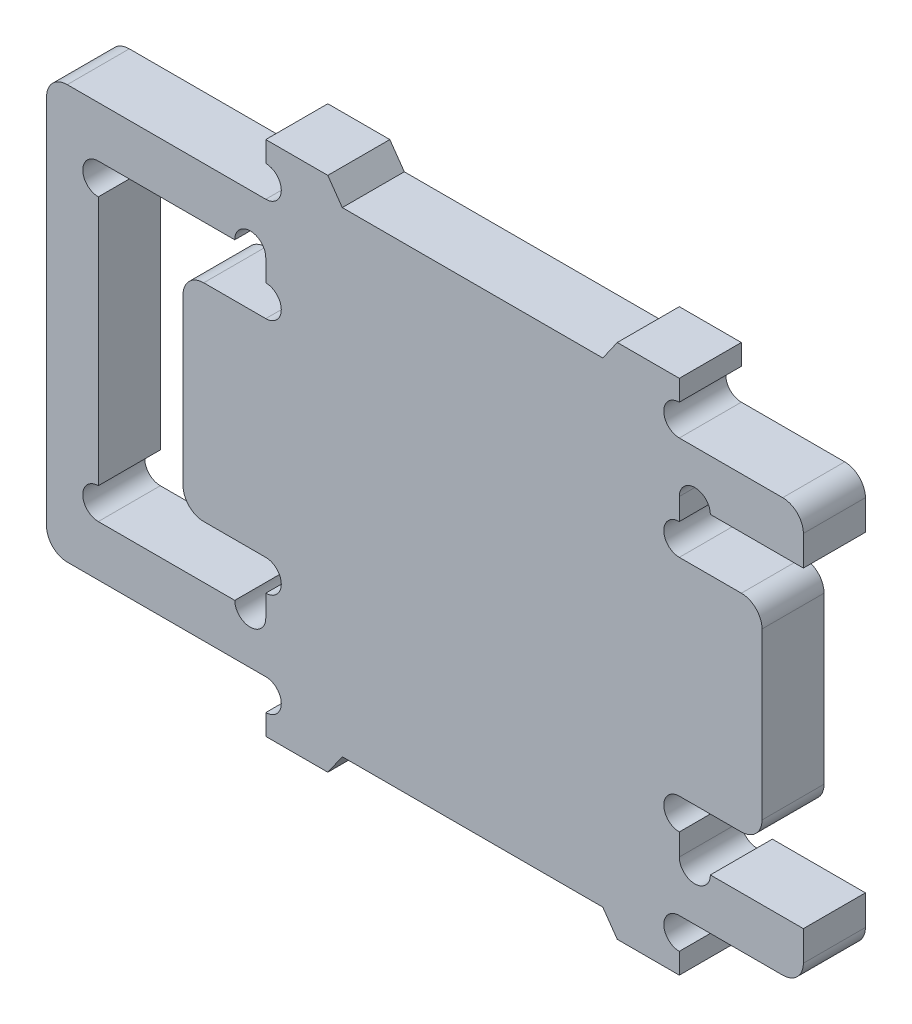
SolidWorks part; units mm, degrees
ref_plane "前视基准面" through (0, 0, 0) normal (0, 0, 1) x (1, 0, 0)
ref_plane "上视基准面" through (0, 0, 0) normal (0, 1, 0) x (1, 0, 0)
ref_plane "右视基准面" through (0, 0, 0) normal (1, 0, 0) x (0, 0, -1)
sketch "草图1" plane through (0, 0, 0) normal (0, 0, 1) x (1, 0, 0)
  line L0 (0, 10) -> (10.6, 10)
  line L1 (0, 10) -> (0, -10)
  line L2 (0, -10) -> (10.6, -10)
  line L3 (6.6, 5) -> (10.6, 5)
  line L4 (6.6, 5) -> (6.6, -5)
  line L5 (6.6, -5) -> (10.6, -5)
  line L6 (2.5, 7.55) -> (10.6, 7.55)
  line L7 (2.5, 7.55) -> (2.5, -7.55)
  line L8 (2.5, -7.55) -> (10.6, -7.55)
  line L9 (10.6, 10) -> (10.6, 12.5)
  line L10 (10.6, 12.5) -> (30.6, 12.5)
  line L11 (30.6, 12.5) -> (30.6, 10)
  line L12 (30.6, 10) -> (36.6, 10)
  line L13 (36.6, 10) -> (36.6, 7.55)
  line L14 (36.6, 7.55) -> (30.6, 7.55)
  line L15 (30.6, 7.55) -> (30.6, 5)
  line L16 (30.6, 5) -> (34.6, 5)
  line L17 (34.6, 5) -> (34.6, -5)
  line L18 (34.6, -5) -> (30.6, -5)
  line L19 (30.6, -5) -> (30.6, -7.55)
  line L20 (30.6, -7.55) -> (36.6, -7.55)
  line L21 (36.6, -7.55) -> (36.6, -10)
  line L22 (36.6, -10) -> (30.6, -10)
  line L23 (30.6, -10) -> (30.6, -12.5)
  line L24 (30.6, -12.5) -> (10.6, -12.5)
  line L25 (10.6, -12.5) -> (10.6, -10)
  line L26 (10.6, -5) -> (10.6, -7.55)
  line L27 (10.6, 7.55) -> (10.6, 5)
  point P2 (0, 0)
  point P14 (2.5, 0)
  point P15 (6.6, 0)
  dimension "D1" = 20
  dimension "D2" = 10
  dimension "D3" = 15.1
  dimension "D4" = 4.1
  dimension "D5" = 4
  dimension "D6" = 20
  dimension "D7" = 4
  dimension "D8" = 2.5
  dimension "D9" = 25
  dimension "D10" = 6
extrude "凸台-拉伸1" add sketch "草图1" along normal mid plane 3
fillet "圆角1" radius 1 8 edges at (0, -10, 0) (0, 10, 0) (6.6, -5, 0) (6.6, 5, 0) (36.6, 10, 0) (36.6, -10, 0) (34.6, -5, 0) (34.6, 5, 0)
sketch "草图3" plane through (0, 0, 1.5) normal (0, 0, 1) x (1, 0, 0)
  line L4 (10.6, 7.55) -> (2.5, 7.55) construction
  line L5 (2.5, -7.55) -> (10.6, -7.55) construction
  line L6 (30.6, 7.55) -> (36.6, 7.55) construction
  line L7 (30.6, 5) -> (30.6, 7.55) construction
  line L8 (30.6, -7.55) -> (30.6, -5) construction
  line L9 (36.6, -7.55) -> (30.6, -7.55) construction
  line L10 (10.6, 5) -> (10.6, 7.55) construction
  line L11 (10.6, -7.55) -> (10.6, -5) construction
  circle A4 centre (9.85, 7.55) radius 0.75
  circle A5 centre (9.85, -7.55) radius 0.75
  circle A6 centre (31.35, 7.55) radius 0.75
  circle A7 centre (30.6, 5.75) radius 0.75
  circle A8 centre (30.6, -5.75) radius 0.75
  circle A9 centre (31.35, -7.55) radius 0.75
  circle A10 centre (10.6, 5.75) radius 0.75
  circle A11 centre (10.6, -5.75) radius 0.75
  dimension "D1" = 1.5
extrude "切除-拉伸1" cut sketch "草图3" against normal through all
sketch "草图4" plane through (0, 0, 1.5) normal (0, 0, 1) x (1, 0, 0)
  line L0 (10.6, 12.5) -> (10.6, 10) construction
  line L1 (30.6, 10) -> (30.6, 12.5) construction
  line L2 (10.6, -10) -> (10.6, -12.5) construction
  line L3 (30.6, -12.5) -> (30.6, -10) construction
  circle A0 centre (10.6, 10.75) radius 0.75
  circle A1 centre (30.6, 10.75) radius 0.75
  circle A2 centre (10.6, -10.75) radius 0.75
  circle A3 centre (30.6, -10.75) radius 0.75
  arc A4 (30.6, -7.55) -> (32.1, -7.55) centre (31.35, -7.55) ccw construction
extrude "切除-拉伸2" cut sketch "草图4" against normal through all
sketch "草图5" plane through (0, 0, 1.5) normal (0, 0, 1) x (1, 0, 0)
  line L0 (2.5, 7.55) -> (2.5, -7.55) construction
  circle A0 centre (2.5, 6.8) radius 0.75
  circle A1 centre (2.5, -6.8) radius 0.75
  arc A2 (10.6, 7.55) -> (9.1, 7.55) centre (9.85, 7.55) ccw construction
extrude "切除-拉伸3" cut sketch "草图5" against normal through all
sketch "草图8" plane through (0, 0, 1.5) normal (0, 0, 1) x (1, 0, 0)
  line L0 (13.6, -12.5) -> (14.3002, -11.5)
  line L1 (10.6, -12.5) -> (30.6, -12.5) construction
  line L2 (14.3002, -11.5) -> (26.8998, -11.5)
  line L3 (26.8998, -11.5) -> (27.6, -12.5)
  line L4 (27.6, -12.5) -> (13.6, -12.5)
  point P4 (20.6, -12.5)
  dimension "D1" = 1
  dimension "D2" = 3
  dimension "D3" = 55
extrude "切除-拉伸6" cut sketch "草图8" against normal through all
mirror "镜向2" about plane through (0, 0, 0) normal (0, 1, 0) of "切除-拉伸6"
